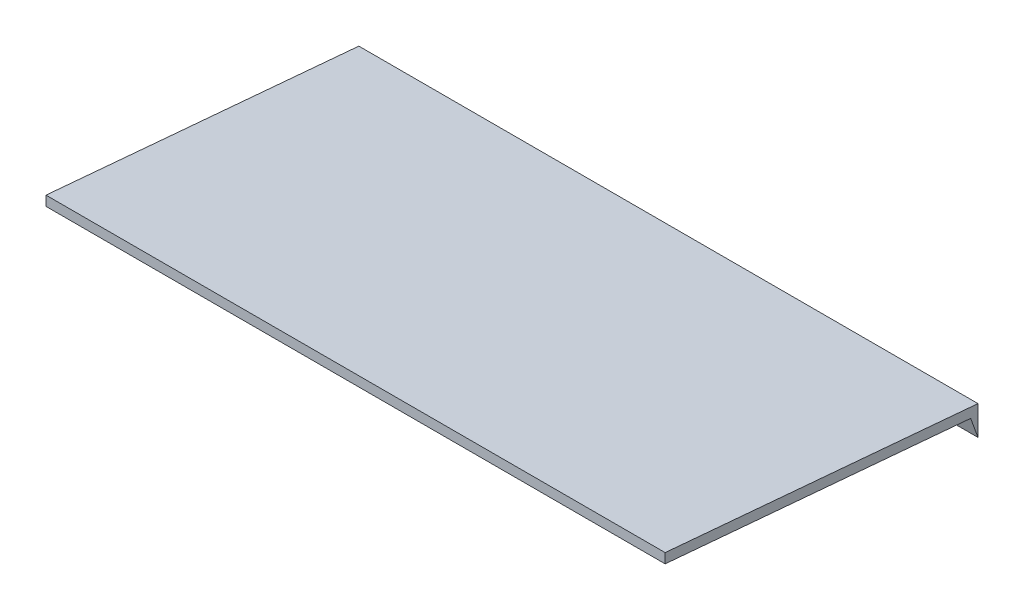
SolidWorks part; units mm, degrees
ref_plane "Front" through (0, 0, 0) normal (0, 0, 1) x (1, 0, 0)
ref_plane "Top" through (0, 0, 0) normal (0, 1, 0) x (1, 0, 0)
ref_plane "Right" through (0, 0, 0) normal (1, 0, 0) x (0, 0, -1)
sketch "Sketch1" plane through (0, 0, 0) normal (1, 0, 0) x (0, 0, -1)
  line L0 (0, 0) -> (3.2, -0.28)
  line L1 (3.2, -0.28) -> (3.2, -0.58)
  line L2 (3.2, -0.58) -> (3.1248, -0.3734)
  line L3 (3.1248, -0.3734) -> (0, -0.1)
  line L4 (0, -0.1) -> (0, 0)
  line L5 (0, 0) -> (15.5783, 0) construction
  dimension "D1" = 20
  dimension "D2" = 5
  dimension "D3" = 0.1
  dimension "D4" = 0.3
  dimension "D5" = 3.2
extrude "Extrude1" add sketch "Sketch1" along normal mid plane 6.3333
ref_plane "point plane" through (0, -0.58, 0) normal (0, 1, 0) x (-1, 0, 0)
